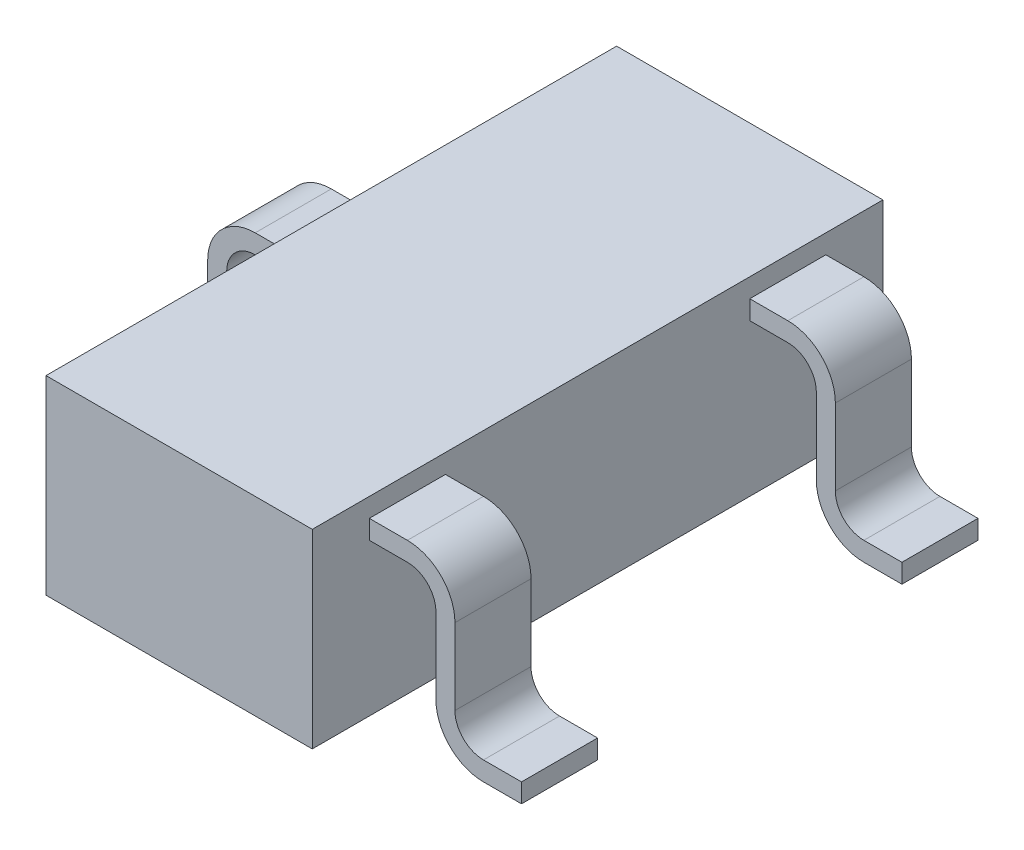
SolidWorks part; units mm, degrees
ref_plane "Front Plane" through (0, 0, 0) normal (0, 0, 1) x (1, 0, 0)
ref_plane "Top Plane" through (0, 0, 0) normal (0, 1, 0) x (1, 0, 0)
ref_plane "Right Plane" through (0, 0, 0) normal (1, 0, 0) x (0, 0, -1)
sketch "BaseS" plane through (0, 0, 0) normal (0, 1, 0) x (1, 0, 0)
  line L1 (-0.7, 1.5) -> (0.7, 1.5)
  line L2 (-0.7, 1.5) -> (-0.7, -1.5)
  line L3 (-0.7, -1.5) -> (0.7, -1.5)
  line L4 (0.7, 1.5) -> (0.7, -1.5)
  line L5 (-0.7, 1.5) -> (0.7, -1.5) construction
  line L6 (-0.7, -1.5) -> (0.7, 1.5) construction
  point P0 (0, 0)
  dimension "Length" = 3
  dimension "Width" = 1.4
extrude "Base" add sketch "BaseS" along normal mid plane 1
ref_plane "LegRP" through (0, 0, 1) normal (0, 0, 1) x (1, 0, 0)
sketch "LegS" plane through (0, 0, 1) normal (0, 0, 1) x (1, 0, 0)
  line L0 (0.7, 0.5) -> (0.7, -0.5) construction
  line L1 (-0.7, -0.5) -> (0.7, -0.5) construction
  line L3 (1.5, -0.45) -> (1.3, -0.45)
  line L4 (1.1, -0.25) -> (1.1, 0.15)
  line L5 (0.7, 0.35) -> (0.9, 0.35)
  line L6 (0.7, 0.5) -> (0.7, -0.5) construction
  arc A2 (1.1, -0.25) -> (1.3, -0.45) centre (1.3, -0.25) ccw
  arc A3 (1.1, 0.15) -> (0.9, 0.35) centre (0.9, 0.15) ccw
  dimension "D3" = 0.2
  dimension "D4" = 0.2
  dimension "D1" = 0.2
  dimension "D2" = 0.2
  dimension "D5" = 0.05
  dimension "Height" = 0.8
extrude "Leg" add sketch "LegS" along normal mid plane 0.4 thin contours L5 A3 L4 A2 L3 thin type mid plane wall 0.1
mirror "Mirror1" about plane through (0, 0, 0) normal (0, 0, 1) of "Leg"
sketch "MidLegS" plane through (0, 0, 0) normal (0, 0, 1) x (1, 0, 0)
  line L0 (1.5, -0.45) -> (1.3, -0.45) construction
  line L1 (1.1, -0.25) -> (1.1, 0.15) construction
  line L2 (0.7, 0.35) -> (0.9, 0.35) construction
  line L3 (1.5, -0.45) -> (1.3, -0.45) construction
  line L4 (1.1, -0.25) -> (1.1, 0.15) construction
  line L5 (0.7, 0.35) -> (0.9, 0.35) construction
  line L6 (0, -0.88) -> (0, 0.88) construction
  line L7 (-0.7, 0.35) -> (-0.9, 0.35)
  line L8 (-1.1, -0.25) -> (-1.1, 0.15)
  line L9 (-1.5, -0.45) -> (-1.3, -0.45)
  arc A0 (1.1, -0.25) -> (1.3, -0.45) centre (1.3, -0.25) ccw construction
  arc A1 (1.1, 0.15) -> (0.9, 0.35) centre (0.9, 0.15) ccw construction
  arc A2 (1.1, -0.25) -> (1.3, -0.45) centre (1.3, -0.25) ccw construction
  arc A3 (1.1, 0.15) -> (0.9, 0.35) centre (0.9, 0.15) ccw construction
  arc A4 (-1.1, 0.15) -> (-0.9, 0.35) centre (-0.9, 0.15) cw
  arc A5 (-1.1, -0.25) -> (-1.3, -0.45) centre (-1.3, -0.25) cw
extrude "MidLeg" add sketch "MidLegS" along normal mid plane 0.4 separate body thin thin type mid plane wall 0.1
